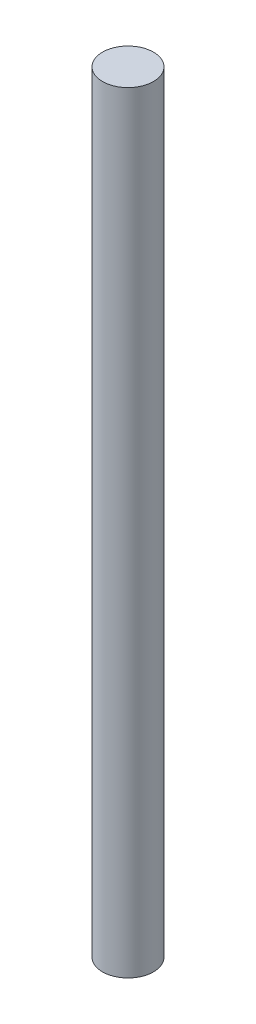
SolidWorks part; units mm, degrees
ref_plane "Front Plane" through (0, 0, 0) normal (0, 0, 1) x (1, 0, 0)
ref_plane "Top Plane" through (0, 0, 0) normal (0, 1, 0) x (1, 0, 0)
ref_plane "Right Plane" through (0, 0, 0) normal (1, 0, 0) x (0, 0, -1)
sketch "Sketch1" plane through (0, 0, 0) normal (0, 1, 0) x (1, 0, 0)
  circle A0 centre (0, 0) radius 3.9
  dimension "D1" = 7.8
extrude "Boss-Extrude1" add sketch "Sketch1" along normal blind 118
